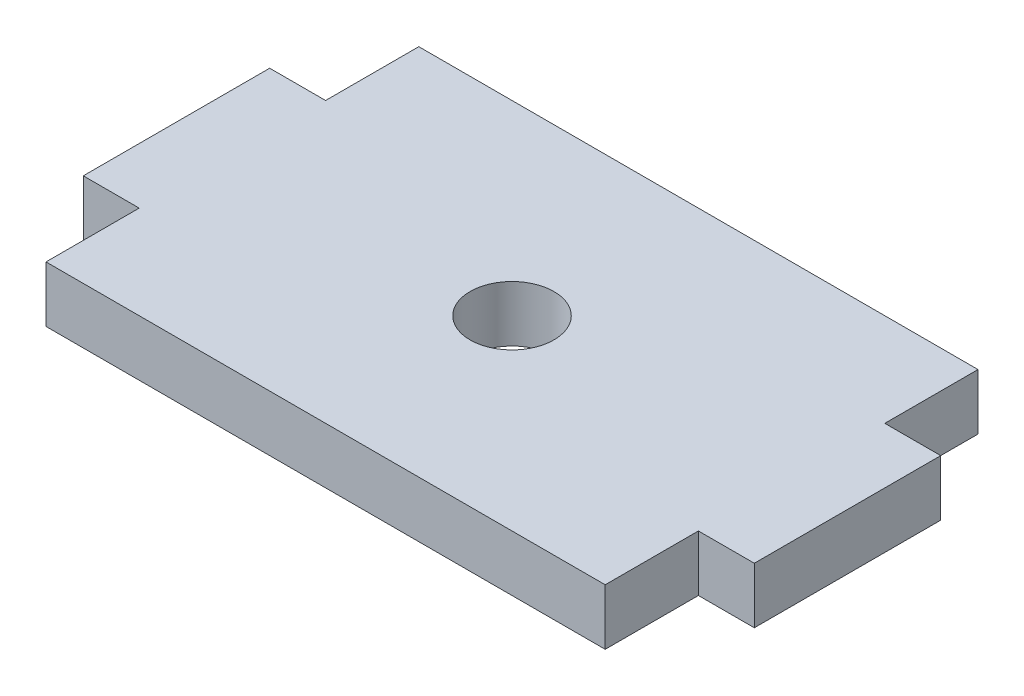
SolidWorks part; units mm, degrees
ref_plane "Front Plane" through (0, 0, 0) normal (0, 0, 1) x (1, 0, 0)
ref_plane "Top Plane" through (0, 0, 0) normal (0, 1, 0) x (1, 0, 0)
ref_plane "Right Plane" through (0, 0, 0) normal (1, 0, 0) x (0, 0, -1)
sketch "Sketch1" plane through (0, 0, 0) normal (0, 1, 0) x (1, 0, 0)
  line L0 (-15, 10) -> (-15, 5)
  line L1 (15, 10) -> (-15, 10)
  line L2 (-15, 5) -> (-18, 5)
  line L3 (15, -10) -> (-15, -10)
  line L4 (-18, 5) -> (-18, -5)
  line L5 (15, 10) -> (-15, -10) construction
  line L6 (15, -10) -> (-15, 10) construction
  line L7 (-18, -5) -> (-15, -5)
  line L8 (-15, -5) -> (-15, -10)
  line L9 (15, -10) -> (15, -5)
  line L10 (15, -5) -> (18, -5)
  line L11 (18, -5) -> (18, 5)
  line L12 (18, 5) -> (15, 5)
  line L13 (15, 5) -> (15, 10)
  circle A0 centre (0, 0) radius 2.25
  point P0 (0, 0)
  dimension "D5" = 4.5
  dimension "D1" = 30
  dimension "D2" = 20
  dimension "D3" = 5
  dimension "D4" = 3
extrude "Boss-Extrude1" add sketch "Sketch1" along normal blind 3
